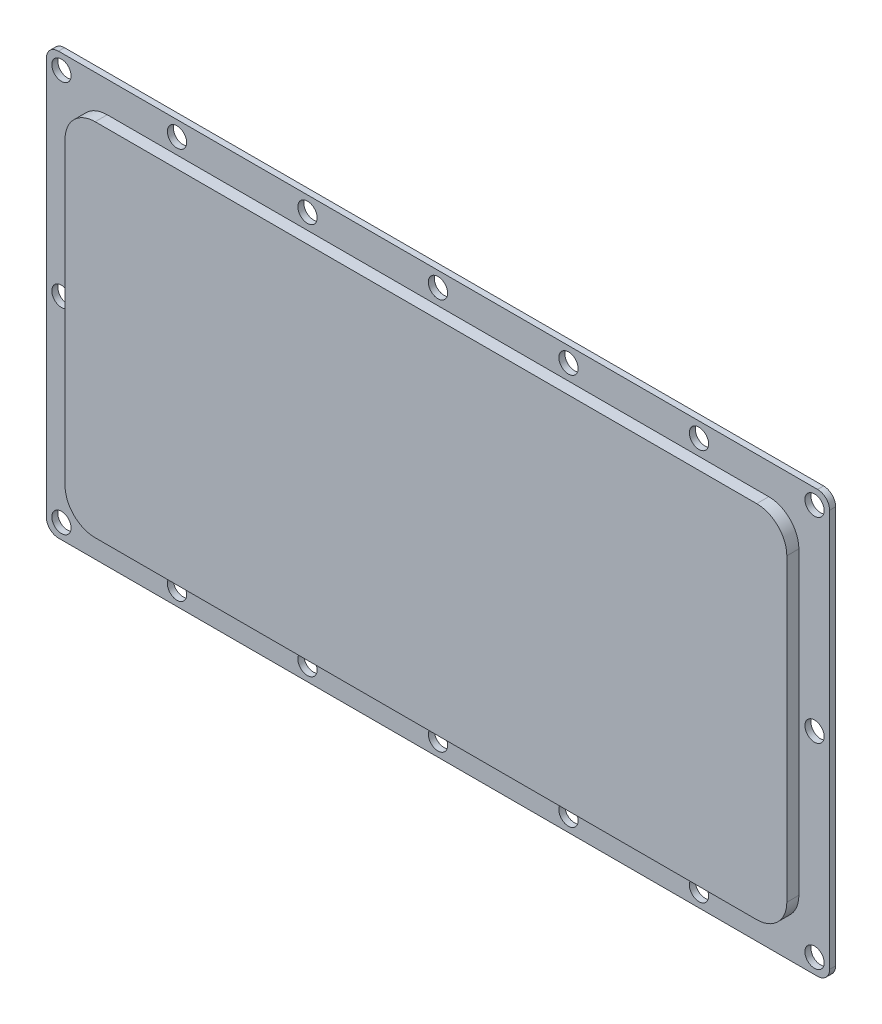
SolidWorks part; units mm, degrees
ref_plane "Plan de face" through (0, 0, 0) normal (0, 0, 1) x (1, 0, 0)
ref_plane "Plan de dessus" through (0, 0, 0) normal (0, 1, 0) x (1, 0, 0)
ref_plane "Plan de droite" through (0, 0, 0) normal (1, 0, 0) x (0, 0, -1)
sketch "Esquisse1" plane through (0, 0, 0) normal (0, 0, 1) x (1, 0, 0)
  line L1 (2, 0) -> (128, 0)
  line L2 (0, 2) -> (0, 68)
  line L3 (2, 70) -> (128, 70)
  line L4 (130, 2) -> (130, 68)
  arc A0 (2, 0) -> (0, 2) centre (2, 2) cw
  arc A1 (128, 0) -> (130, 2) centre (128, 2) ccw
  arc A2 (128, 70) -> (130, 68) centre (128, 68) cw
  arc A3 (0, 68) -> (2, 70) centre (2, 68) cw
  point P7 (0, 0)
  point P12 (130, 70)
  point P15 (0, 70)
  dimension "D3" = 2
  dimension "D1" = 130
  dimension "D2" = 70
extrude "Boss.-Extru.1" add sketch "Esquisse1" along normal blind 1
sketch "Esquisse2" plane through (0, 0, 1) normal (0, 0, 1) x (1, 0, 0)
  line L9 (128, 70) -> (2, 70) construction
  line L10 (10.1, 64.9) -> (119.9, 64.9)
  line L11 (5.1, 59.9) -> (5.1, 10.1)
  line L12 (10.1, 5.1) -> (119.9, 5.1)
  line L13 (124.9, 59.9) -> (124.9, 10.1)
  line L14 (130, 2) -> (130, 68) construction
  line L15 (2, 0) -> (128, 0) construction
  line L16 (0, 68) -> (0, 2) construction
  arc A0 (119.9, 64.9) -> (124.9, 59.9) centre (119.9, 59.9) cw
  arc A1 (119.9, 5.1) -> (124.9, 10.1) centre (119.9, 10.1) ccw
  arc A2 (5.1, 10.1) -> (10.1, 5.1) centre (10.1, 10.1) ccw
  arc A3 (10.1, 64.9) -> (5.1, 59.9) centre (10.1, 59.9) ccw
  dimension "D1" = 5
  dimension "D2" = 5.1
  dimension "5.1" = 5.1
  dimension "D3" = 5.1
  dimension "D4" = 5.1
extrude "Boss.-Extru.2" add sketch "Esquisse2" along normal blind 2
sketch "Esquisse3" plane through (0, 0, 0) normal (0, 0, -1) x (-1, 0, 0)
  line L0 (-137.8282, 67.5) -> (-2.5, 67.5) construction
  line L1 (-2.5, 67.5) -> (-2.5, 2.5) construction
  line L2 (-2.5, 2.5) -> (-127.5, 2.5) construction
  line L3 (-127.5, 2.5) -> (-127.5, 82.8738) construction
  line L4 (-130, 2) -> (-130, 68) construction
  line L5 (-128, 70) -> (-2, 70) construction
  line L6 (0, 68) -> (0, 2) construction
  line L7 (-2, 0) -> (-128, 0) construction
  line L8 (-108.32, 82.8738) -> (-108.32, -9.4063) construction
  line L9 (-65, 82.8738) -> (-65, -9.4063) construction
  line L10 (-86.66, 82.8738) -> (-86.66, -9.4063) construction
  line L11 (-43.34, 82.8738) -> (-43.34, -9.4063) construction
  line L12 (-21.68, 82.8738) -> (-21.68, -9.4063) construction
  line L13 (-137.8282, 35) -> (11.2808, 35) construction
  circle A0 centre (-65, 67.5) radius 1.6
  circle A1 centre (-43.34, 67.5) radius 1.6
  circle A2 centre (-21.68, 67.5) radius 1.6
  circle A3 centre (-2.5, 67.5) radius 1.6
  circle A4 centre (-2.5, 2.5) radius 1.6
  circle A5 centre (-21.68, 2.5) radius 1.6
  circle A6 centre (-43.34, 2.5) radius 1.6
  circle A7 centre (-65, 2.5) radius 1.6
  circle A8 centre (-86.66, 2.5) radius 1.6
  circle A9 centre (-108.32, 2.5) radius 1.6
  circle A10 centre (-127.5, 2.5) radius 1.6
  circle A11 centre (-127.5, 67.5) radius 1.6
  circle A12 centre (-108.32, 67.5) radius 1.6
  circle A13 centre (-86.66, 67.5) radius 1.6
  circle A14 centre (-2.5, 35) radius 1.6
  circle A15 centre (-127.5, 35) radius 1.6
  dimension "D10" = 35
  dimension "D1" = 2.5
  dimension "D2" = 2.5
  dimension "D3" = 2.5
  dimension "D4" = 2.5
  dimension "D5" = 65
  dimension "D6" = 21.66
  dimension "D7" = 21.66
  dimension "D8" = 21.66
  dimension "D9" = 21.66
extrude "Enlèv. mat.-Extru.1" cut sketch "Esquisse3" against normal up to next
